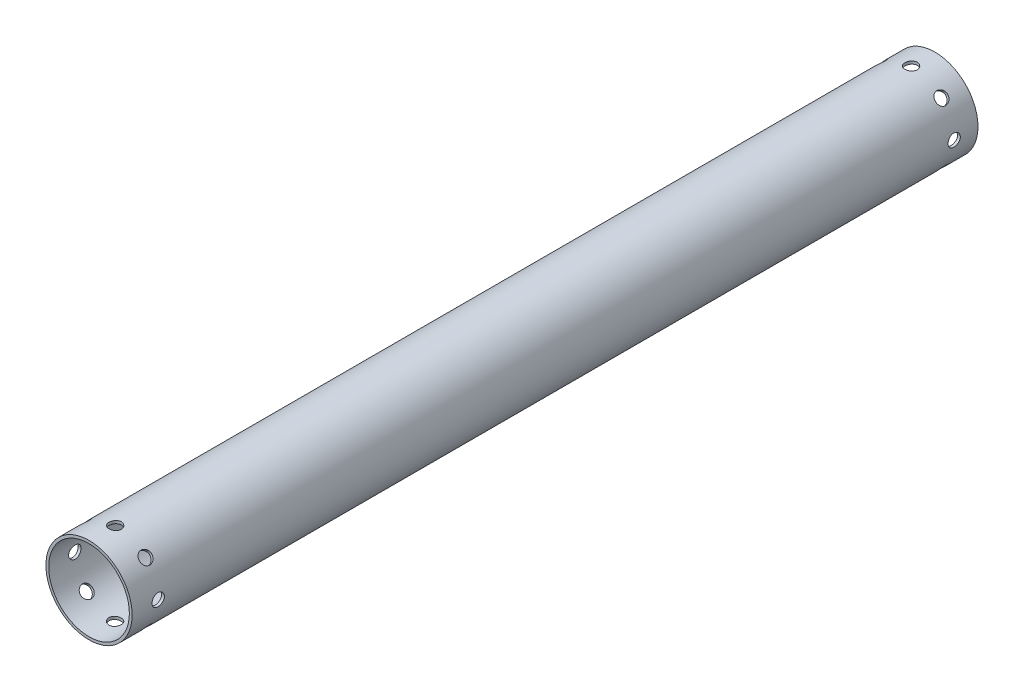
SolidWorks part; units mm, degrees
material "ASTM A53 Grade B"
ref_plane "Front Plane" through (0, 0, 0) normal (0, 0, 1) x (1, 0, 0)
ref_plane "Top Plane" through (0, 0, 0) normal (0, 1, 0) x (1, 0, 0)
ref_plane "Right Plane" through (0, 0, 0) normal (1, 0, 0) x (0, 0, -1)
sketch "Croquis1" plane through (0, 0, 0) normal (0, 0, 1) x (1, 0, 0)
  circle A0 centre (0, 0) radius 26.2509
  circle A1 centre (0, 0) radius 28.0509
  dimension "D1" = 52.5018
  dimension "D2" = 56.1018
extrude "Saliente-Extruir1" add sketch "Croquis1" against normal blind 550.5
sketch "Croquis2" plane through (0, 0, 0) normal (0, 0, 1) x (1, 0, 0)
  circle A0 centre (0, 0) radius 30.1625
  circle A3 centre (0, 0) radius 28.0509 construction
  circle A4 centre (0, 0) radius 28.0509
  dimension "D1" = 60.325
sketch "Croquis3" plane through (0, 0, 0) normal (1, 0, 0) x (0, 0, -1)
  line L0 (550.5, 28.0509) -> (535, 28.0509) construction
  point P4 (535, 28.0509)
  dimension "D1" = 15.5
sketch "Croquis14" plane through (0, 0, 0) normal (1, 0, 0) x (0, 0, -1)
  line L0 (550.5, 28.0509) -> (0, 28.0509) construction
  point P0 (17, 28.0509)
  dimension "D1" = 17
hole_wizard "Ø8.0mm Dowel Hole1" positions "Croquis3D7" profile "Croquis13" hole size "Ø8.0" standard "ANSI Metric"
sketch3d "Croquis3D7"
  point P0 (0, 28.0509, -535)
sketch "Croquis13" plane through (0, 28.0509, -535) normal (1, 0, 0) x (0, 0, 1)
  line L0 (0, 0) -> (0, 9.4034)
  line L1 (0, 9.4034) -> (4, 7)
  line L2 (4, 7) -> (4, 0)
  line L5 (4, 0) -> (0, 0)
  line L10 (0, 9.4034) -> (-4, 7) construction
  line L11 (0, -6.35) -> (0, 107.95) construction
  dimension "Hole Dia." = 8
  dimension "Hole Depth" = 7
  dimension "Drill Angle" = 118
hole_wizard "Ø8.0mm Dowel Hole2" positions "Croquis3D10" profile "Croquis17" hole size "Ø8.0" standard "ANSI Metric"
sketch3d "Croquis3D10"
  point P0 (0, 28.0509, -17)
sketch "Croquis17" plane through (0, 28.0509, -17) normal (1, 0, 0) x (0, 0, 1)
  line L0 (0, 0) -> (0, 9.4034)
  line L1 (0, 9.4034) -> (4, 7)
  line L2 (4, 7) -> (4, 0)
  line L5 (4, 0) -> (0, 0)
  line L10 (0, 9.4034) -> (-4, 7) construction
  line L11 (0, -6.35) -> (0, 107.95) construction
  dimension "Hole Dia." = 8
  dimension "Hole Depth" = 7
  dimension "Drill Angle" = 118
pattern_circular "MatrizC1" count 8 over 360 about axis through (0, 0, -550.5) along (0, 0, 1) of "Ø8.0mm Dowel Hole1", "Ø8.0mm Dowel Hole2"
equation "\"IDcase\"= 52.5018"
equation "\"D1@Croquis1\"=\"IDcase\""
equation "\"ODcase\"= \"IDcase\" + 2 * \"CaseThickness\""
equation "\"D2@Croquis1\"=\"ODcase\""
equation "\"CaseLength\"= 525mm + 25 + 0.5"
equation "\"D1@Saliente-Extruir1\"=\"CaseLength\""
equation "\"CaseThickness\"= 1.8mm"
equation "\"D1@Croquis2\"=2.375in"
equation "\"NozzleScrewLoc\"=15.5"
equation "\"D1@Croquis3\"=\"NozzleScrewLoc\""
equation "\"HeadCaseScrewLoc\"=17"
equation "\"D1@Saliente-Extruir2\"=\"CaseLength\""
